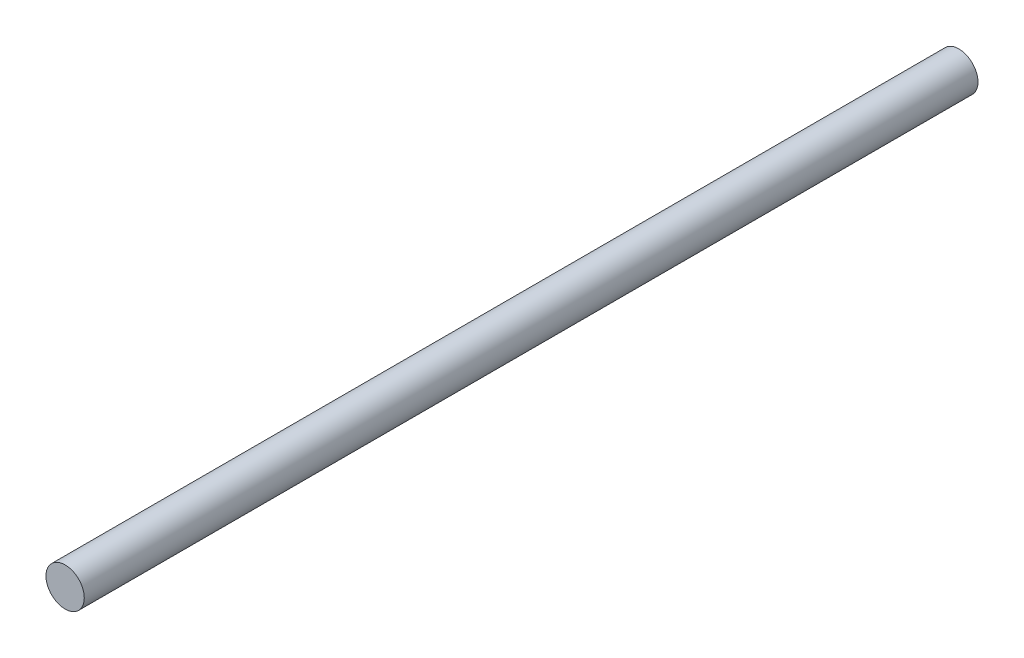
SolidWorks part; units mm, degrees
ref_plane "正面" through (0, 0, 0) normal (0, 0, 1) x (1, 0, 0)
ref_plane "平面" through (0, 0, 0) normal (0, 1, 0) x (1, 0, 0)
ref_plane "右側面" through (0, 0, 0) normal (1, 0, 0) x (0, 0, -1)
sketch "ｽｹｯﾁ1" plane through (0, 0, 0) normal (0, 0, 1) x (1, 0, 0)
  circle A0 centre (0, 0) radius 3
  dimension "D1" = 6
extrude "ﾎﾞｽ - 押し出し1" add sketch "ｽｹｯﾁ1" along normal blind 140
